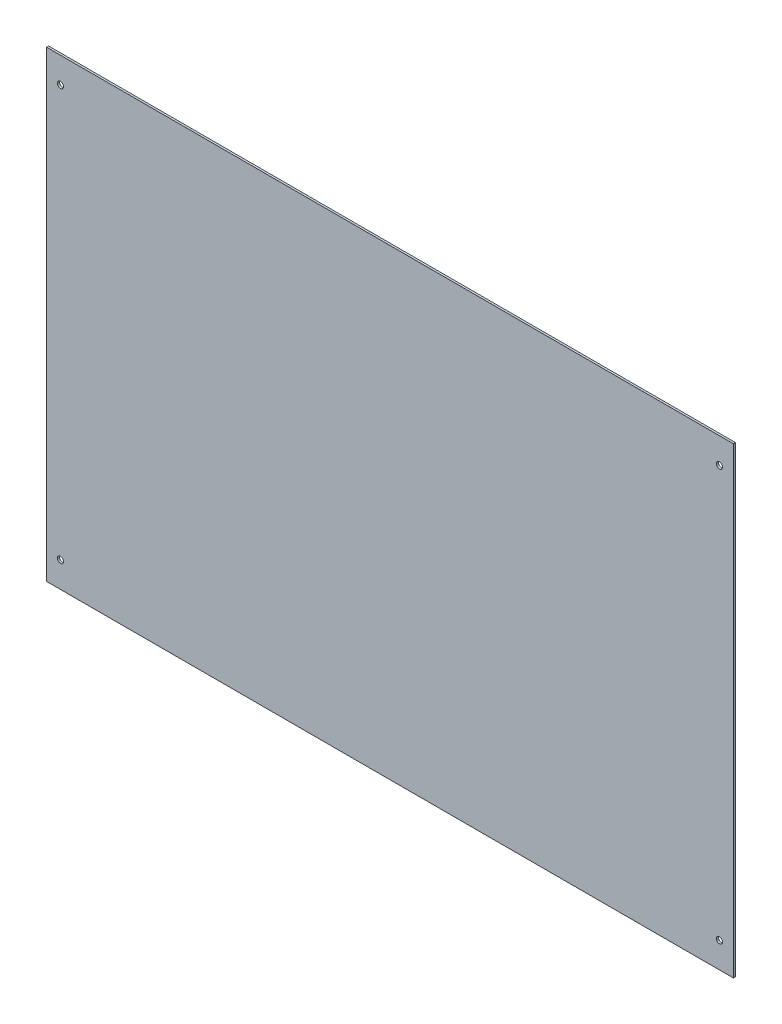
SolidWorks part; units mm, degrees
ref_plane "Front Plane" through (0, 0, 0) normal (0, 0, 1) x (1, 0, 0)
ref_plane "Top Plane" through (0, 0, 0) normal (0, 1, 0) x (1, 0, 0)
ref_plane "Right Plane" through (0, 0, 0) normal (1, 0, 0) x (0, 0, -1)
sketch "Sketch1" plane through (0, 0, 0) normal (0, 0, 1) x (1, 0, 0)
  line L1 (334, -225) -> (-334, -225)
  line L2 (334, -225) -> (334, 225)
  line L3 (334, 225) -> (-334, 225)
  line L4 (-334, -225) -> (-334, 225)
  line L5 (334, -225) -> (-334, 225) construction
  line L6 (334, 225) -> (-334, -225) construction
  point P0 (0, 0)
  dimension "D1" = 668
  dimension "D2" = 450
extrude "Extrude1" add sketch "Sketch1" along normal blind 2
sketch "Sketch3" plane through (0, 0, 2) normal (0, 0, 1) x (1, 0, 0)
  circle A0 centre (-320.427, 200) radius 3
  circle A1 centre (-320.427, -200) radius 3
  circle A2 centre (320.427, -200) radius 3
  circle A3 centre (320.427, 200) radius 3
  dimension "D1" = 6
extrude "Cut-Extrude1" cut sketch "Sketch3" against normal through all
sketch "Sketch5" plane through (0, 0, 0) normal (0, 0, -1) x (-1, 0, 0)
  text T0 "Domestic\r\nAirport" font "AG Stencil" height 50
extrude "Extrude4" cut sketch "Sketch5" against normal blind 1
